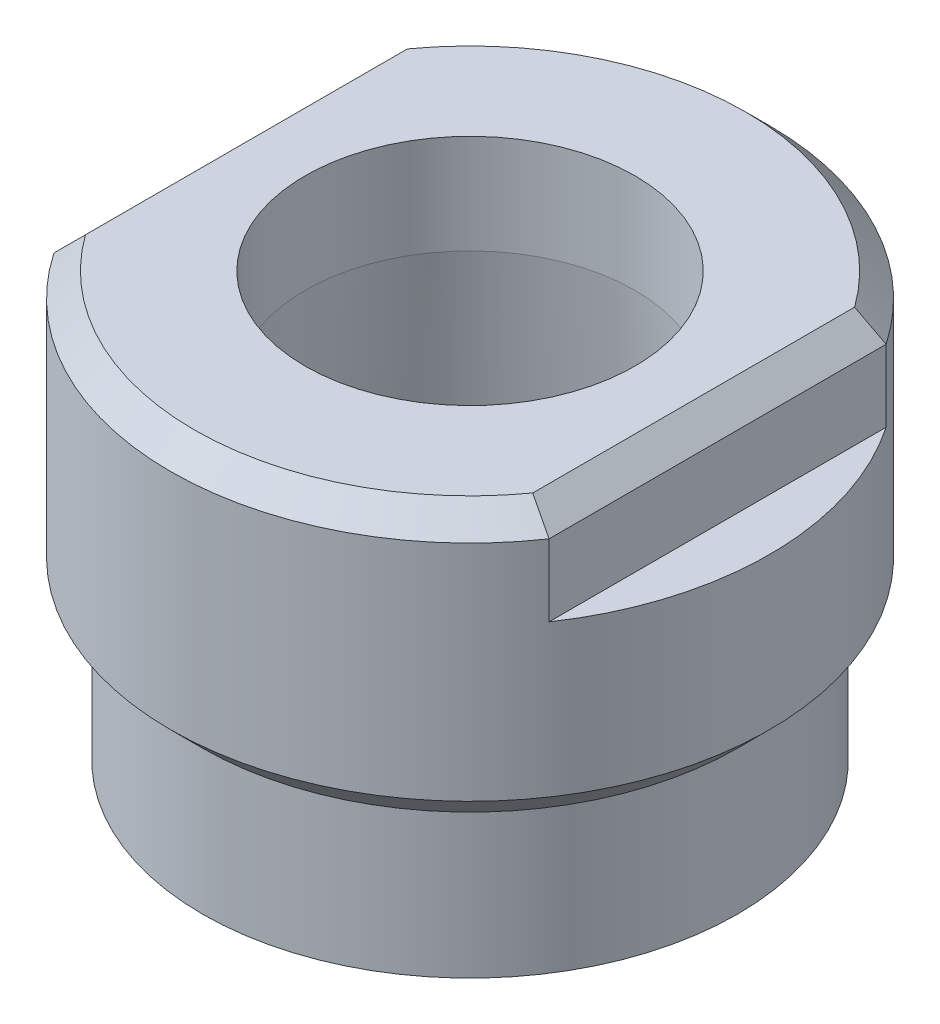
SolidWorks part; units mm, degrees
material "Brass"
ref_plane "Front Plane" through (0, 0, 0) normal (0, 0, 1) x (1, 0, 0)
ref_plane "Top Plane" through (0, 0, 0) normal (0, 1, 0) x (1, 0, 0)
ref_plane "Right Plane" through (0, 0, 0) normal (1, 0, 0) x (0, 0, -1)
sketch "Sketch1" plane through (0, 0, 0) normal (0, 0, 1) x (1, 0, 0)
  line L0 (0, 0) -> (0, -75.6659) construction
  line L1 (-5.2451, -1.8858) -> (-5.969, -10.16)
  line L2 (-5.969, -10.16) -> (-8.001, -12.192)
  line L3 (-8.001, -12.192) -> (-8.509, -12.192)
  line L4 (-9.525, -6.604) -> (-9.525, 0.508)
  line L5 (-8.509, -7.62) -> (-9.525, -6.604)
  line L6 (-5.2451, 0) -> (-5.2451, -1.8858)
  line L7 (-9.525, 0.508) -> (-8.763, 1.27)
  line L11 (-8.509, -7.62) -> (-8.509, -12.192)
  line L12 (-8.763, 1.27) -> (-5.2451, 1.27)
  line L13 (-5.2451, 1.27) -> (-5.2451, 0)
  dimension "D1" = 5
  dimension "D2" = 45
  dimension "D3" = 1.27
  dimension "D4" = 2.032
  dimension "D5" = 0.762
  dimension "D6" = 19.05
  dimension "D7" = 10.4902
  dimension "D8" = 17.018
  dimension "D9" = 7.112
  dimension "D10" = 0.508
  dimension "D11" = 12.192
  dimension "D12" = 45
revolve "Revolve1" add sketch "Sketch1" angle 360 about L0
sketch "Sketch2" plane through (0, 0, 0) normal (0, 0, 1) x (1, 0, 0)
  line L0 (0, 4.6495) -> (0, -14.2374) construction
  line L1 (8.763, 1.27) -> (-8.763, 1.27) construction
  line L2 (-7.874, 1.27) -> (-9.525, 1.27)
  line L3 (-7.874, 1.27) -> (-7.874, -1.778)
  line L4 (-7.874, -1.778) -> (-9.525, -1.778)
  line L5 (-9.525, 1.27) -> (-9.525, -1.778)
  line L6 (-9.525, 0.508) -> (-9.525, -6.604) construction
  line L7 (9.525, 1.27) -> (9.525, -1.778)
  line L8 (7.874, -1.778) -> (9.525, -1.778)
  line L9 (7.874, 1.27) -> (7.874, -1.778)
  line L10 (7.874, 1.27) -> (9.525, 1.27)
  dimension "D1" = 15.748
  dimension "D2" = 3.048
extrude "Cut-Extrude1" cut sketch "Sketch2" against normal through all and the other way through all
chamfer "Chamfer1" distance 0.762 angle 45 2 edges at (7.874, 1.27, 0) (-7.874, 1.27, 0)
